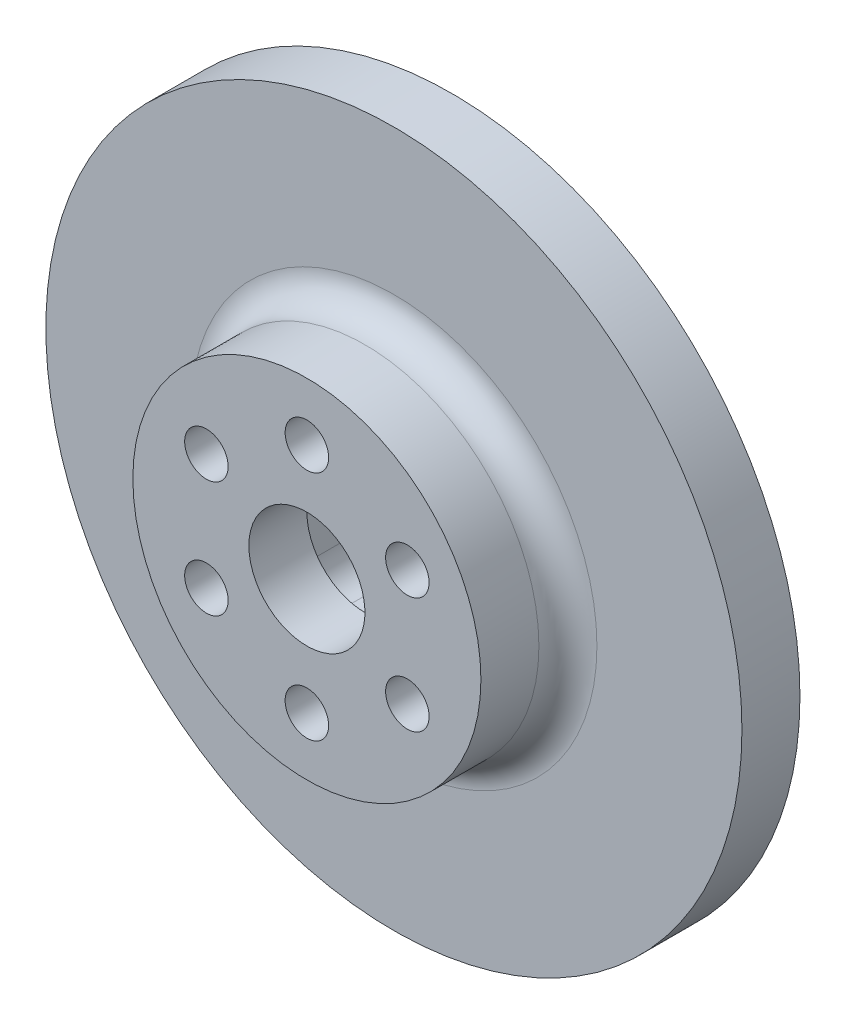
SolidWorks part; units mm, degrees
material "Plain Carbon Steel"
ref_plane "Front" through (0, 0, 0) normal (0, 0, 1) x (1, 0, 0)
ref_plane "Top" through (0, 0, 0) normal (0, 1, 0) x (1, 0, 0)
ref_plane "Right" through (0, 0, 0) normal (1, 0, 0) x (0, 0, -1)
sketch "Sketch1" plane through (0, 0, 0) normal (0, 0, 1) x (1, 0, 0)
  circle A0 centre (0, 0) radius 38.1
  point P14 (0, 0)
  dimension "D1" = 76.2
extrude "Boss-Extrude1" add sketch "Sketch1" along normal blind 6.35
sketch "Sketch2" plane through (0, 0, 6.35) normal (0, 0, 1) x (1, 0, 0)
  circle A0 centre (0, 0) radius 19.05
  circle A2 centre (0, 0) radius 19.05 construction
extrude "Boss-Extrude2" add sketch "Sketch2" along normal up to surface (9.525 mm away)
sketch "Sketch3" plane through (0, 0, 0) normal (0, 0, -1) x (-1, 0, 0)
  line L1 (-4.7625, -9.525) -> (4.7625, -9.525)
  line L2 (-7.9375, -6.35) -> (-7.9375, 6.35)
  line L3 (-4.7625, 9.525) -> (4.7625, 9.525)
  line L4 (7.9375, -6.35) -> (7.9375, 6.35)
  line L5 (0, 9.525) -> (0, -9.525) construction
  line L6 (-7.9375, 0) -> (7.9375, 0) construction
  circle A0 centre (0, 0) radius 9.8425 construction
  arc A1 (-4.7625, -9.525) -> (-7.9375, -6.35) centre (-4.7625, -6.35) cw
  arc A2 (4.7625, -9.525) -> (7.9375, -6.35) centre (4.7625, -6.35) ccw
  arc A3 (4.7625, 9.525) -> (7.9375, 6.35) centre (4.7625, 6.35) cw
  arc A4 (-7.9375, 6.35) -> (-4.7625, 9.525) centre (-4.7625, 6.35) cw
  dimension "D1" = 19.685
  dimension "D3" = 3.175
  dimension "D2" = 15.875
  dimension "D4" = 19.05
extrude "Cut-Extrude1" cut sketch "Sketch3" against normal up to surface (9.525 mm away)
sketch "Sketch4" plane through (0, 0, 9.525) normal (0, 0, -1) x (-1, 0, 0)
  circle A0 centre (0, 0) radius 6.35
  dimension "D1" = 12.7
extrude "Cut-Extrude2" cut sketch "Sketch4" against normal through all
sketch "Sketch7" plane through (0, 0, 15.875) normal (0, 0, 1) x (1, 0, 0)
  circle A0 centre (0, 12.7) radius 2.3813
  circle A1 centre (0, 12.7) radius 2.3813 construction
  circle A2 centre (10.9985, 6.35) radius 2.3813
  circle A3 centre (10.9985, -6.35) radius 2.3813
  circle A4 centre (0, -12.7) radius 2.3813
  circle A5 centre (-10.9985, -6.35) radius 2.3813
  circle A6 centre (-10.9985, 6.35) radius 2.3813
  circle A7 centre (0, 0) radius 6.35 construction
  point P17 (0, 0)
  dimension "D1" = 6
fillet "Fillet2" radius 3.175 1 edges at (19.05, 0, 6.35)
extrude "Cut-Extrude4" cut sketch "Sketch7" against normal blind 6.35
